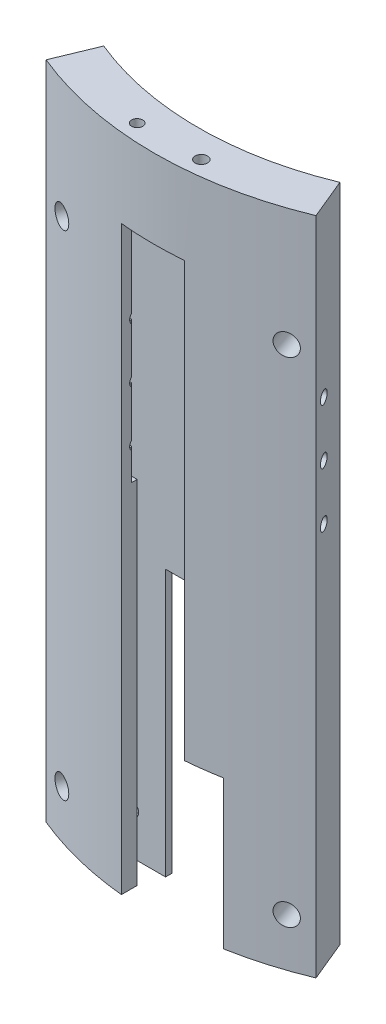
SolidWorks part; units mm, degrees
ref_plane "Front Plane" through (0, 0, 0) normal (0, 0, 1) x (1, 0, 0)
ref_plane "Top Plane" through (0, 0, 0) normal (0, 1, 0) x (1, 0, 0)
ref_plane "Right Plane" through (0, 0, 0) normal (1, 0, 0) x (0, 0, -1)
sketch "Sketch1" plane through (0, 0, 0) normal (0, 1, 0) x (1, 0, 0)
  line L1 (-23.1, -13.65) -> (23.1, -13.65)
  line L2 (-23.1, -13.65) -> (-23.1, 13.65)
  line L3 (-23.1, 13.65) -> (23.1, 13.65)
  line L4 (23.1, -13.65) -> (23.1, 13.65)
  line L5 (-23.1, -13.65) -> (23.1, 13.65) construction
  line L6 (-23.1, 13.65) -> (23.1, -13.65) construction
  point P0 (0, 0)
extrude "Boss-Extrude1" add sketch "Sketch1" along normal blind 107
sketch "Sketch2" plane through (0, 0, 0) normal (0, -1, 0) x (1, 0, 0)
  line L0 (-5.5, 3.65) -> (4.8, 3.65)
  line L5 (-13.1, 1.25) -> (-13.1, -2.25)
  line L6 (-4.4, -3.65) -> (13.1, -3.65)
  line L7 (-4.4, -3.65) -> (-4.4, -2.25)
  line L8 (-4.4, -2.25) -> (-13.1, -2.25)
  line L9 (13.1, -2.15) -> (13.1, -3.65)
  line L10 (-13.1, 1.25) -> (-5.5, 1.25)
  line L11 (-5.5, 1.25) -> (-5.5, 3.65)
  line L13 (4.8, 3.65) -> (4.8, 3.05)
  line L14 (4.8, 3.05) -> (10.4, 3.05)
  line L15 (10.4, 3.05) -> (10.4, 0.45)
  line L16 (10.4, 0.45) -> (11.7, 0.45)
  line L17 (11.7, 0.45) -> (11.7, -2.15)
  line L18 (11.7, -2.15) -> (13.1, -2.15)
  point P0 (0, 0)
extrude "Cut-Extrude1" cut sketch "Sketch2" against normal blind 24
sketch "Sketch3" plane through (0, 24, 0) normal (0, -1, 0) x (1, 0, 0)
  line L0 (-13.1, 1.25) -> (-13.1, -2.25)
  line L1 (-13.1, -2.25) -> (-4.4, -2.25)
  line L2 (-4.4, -2.25) -> (-4.4, -3.65)
  line L3 (-4.4, -3.65) -> (13.1, -3.65)
  line L4 (13.1, -3.65) -> (13.1, -2.15)
  line L5 (13.1, -2.15) -> (11.7, -2.15)
  line L6 (11.7, 0.45) -> (10.4, 0.45)
  line L7 (11.7, 0.45) -> (11.7, -2.15)
  line L8 (10.4, 0.45) -> (10.4, 2.15)
  line L10 (10.4, 0.45) -> (10.4, 3.05) construction
  line L11 (10.4, 2.15) -> (4.8, 2.15)
  line L12 (4.8, 2.15) -> (4.8, 3.65)
  line L13 (4.8, 3.65) -> (-5.5, 3.65)
  line L14 (-5.5, 3.65) -> (-5.5, 1.25)
  line L15 (-13.1, 1.25) -> (-5.5, 1.25)
extrude "Cut-Extrude2" cut sketch "Sketch3" against normal blind 19.2
sketch "Sketch4" plane through (0, 43.2, 0) normal (0, -1, 0) x (1, 0, 0)
  line L0 (-13.1, -2.25) -> (11.7, -2.25)
  line L1 (-13.1, -2.25) -> (-13.1, -0.55)
  line L2 (-13.1, 1.25) -> (-13.1, -2.25) construction
  line L3 (-13.1, -0.55) -> (-9.3, -0.55)
  line L4 (-9.3, -0.55) -> (-9.3, 1.25)
  line L5 (-9.3, 1.25) -> (-5.5, 1.25)
  line L6 (-5.5, 1.25) -> (-5.5, 3.65)
  line L7 (-5.5, 3.65) -> (4.8, 3.65)
  line L8 (4.8, 3.65) -> (4.8, 1.15)
  line L9 (4.8, 1.15) -> (8.9, 1.15)
  line L10 (8.9, 1.15) -> (8.9, -0.55)
  line L11 (8.9, -0.55) -> (11.7, -0.55)
  line L12 (11.7, -2.15) -> (11.7, 0.45) construction
  line L13 (11.7, -0.55) -> (11.7, -2.25)
extrude "Cut-Extrude3" cut sketch "Sketch4" against normal blind 50
sketch "Sketch5" plane through (0, 93.2, 0) normal (0, -1, 0) x (1, 0, 0)
  line L0 (-13.1, -2.25) -> (11.7, -2.25)
  line L1 (11.7, -2.25) -> (11.7, -0.55)
  line L2 (-5.5, 3.65) -> (4.8, 3.65)
  line L3 (4.8, 3.65) -> (4.8, -0.55)
  line L4 (4.8, -0.55) -> (11.7, -0.55)
  line L5 (-5.5, 3.65) -> (-5.5, -0.55)
  line L6 (-5.5, -0.55) -> (-13.1, -0.55)
  line L7 (-13.1, -0.55) -> (-13.1, -2.25)
extrude "Cut-Extrude4" cut sketch "Sketch5" against normal blind 1
sketch "Sketch6" plane through (0, 94.2, 0) normal (0, -1, 0) x (1, 0, 0)
  line L1 (-13.1, -0.55) -> (11.7, -0.55)
  line L2 (-13.1, -0.55) -> (-13.1, -2.25)
  line L3 (-13.1, -2.25) -> (11.7, -2.25)
  line L4 (11.7, -0.55) -> (11.7, -2.25)
extrude "Cut-Extrude5" cut sketch "Sketch6" against normal blind 5.48
fillet "Fillet1" radius 3.1 2 edges at (11.7, 99.68, -1.4) (-13.1, 99.68, -1.4)
sketch "Sketch7" plane through (-23.1, 0, 0) normal (-1, 0, 0) x (0, 0, 1)
  line L1 (13.65, 107) -> (-13.65, 107)
  line L2 (13.65, 107) -> (13.65, 0)
  line L3 (13.65, 0) -> (-13.65, 0)
  line L4 (-13.65, 107) -> (-13.65, 0)
extrude "Boss-Extrude2" add sketch "Sketch7" along normal blind 35.75
sketch "Sketch8" plane through (23.1, 0, 0) normal (1, 0, 0) x (0, 0, -1)
  line L1 (-13.65, 107) -> (13.65, 107)
  line L2 (-13.65, 107) -> (-13.65, 0)
  line L3 (-13.65, 0) -> (13.65, 0)
  line L4 (13.65, 107) -> (13.65, 0)
extrude "Boss-Extrude3" add sketch "Sketch8" along normal blind 35.75
sketch "Sketch9" plane through (0, 0, -13.65) normal (0, 0, -1) x (-1, 0, 0)
  line L1 (-58.85, 0) -> (58.85, 0)
  line L2 (-58.85, 0) -> (-58.85, 107)
  line L3 (-58.85, 107) -> (58.85, 107)
  line L4 (58.85, 0) -> (58.85, 107)
extrude "Boss-Extrude4" add sketch "Sketch9" along normal blind 39.2125
sketch "Sketch10" plane through (0, 0, 0) normal (0, -1, 0) x (1, 0, 0)
  line L2 (-19.0342, -6.8685) -> (-21.7704, -0.2628)
  line L3 (19.2342, -6.8685) -> (21.9704, -0.2628)
  arc A1 (21.9704, -0.2628) -> (-21.7704, -0.2628) centre (0.1, -53.0625) ccw
  arc A2 (19.2342, -6.8685) -> (-19.0342, -6.8685) centre (0.1, -53.0625) ccw
  dimension "D1" = 45
extrude "Cut-Extrude6" cut sketch "Sketch10" against normal up to vertex (107 mm away) flip side to cut
sketch "Sketch14" plane through (-18.6751, 0, -7.7355) normal (-0.9239, 0, -0.3827) x (-0.3827, 0, 0.9239)
  line L0 (5.7509, 80) -> (0.9384, 80)
  line L2 (-49.0616, 107) -> (-49.0616, 73.6066)
  line L3 (0.9384, 107) -> (0.9384, 0) construction
  circle A0 centre (5.7509, 80) radius 1
  circle A1 centre (5.7509, 71.1) radius 1
  circle A2 centre (5.7509, 62.2) radius 1
  dimension "D1" = 3
  dimension "D2" = 2
revolve "Cut-Revolve1" cut sketch "Sketch14" angle 360 about L2
sketch "Sketch15" plane through (0, 107, 0) normal (0, 1, 0) x (1, 0, 0)
  circle A0 centre (4.8, -1.15) radius 1
  circle A1 centre (-5.5, -1.25) radius 0.9
extrude "Cut-Extrude7" cut sketch "Sketch15" against normal blind 50
ref_plane "Plane3" through (-2.157, 0, 6.4466) normal (-0.3173, 0, 0.9483) x (0, -1, 0)
sketch "Sketch19" plane through (-18.6751, 0, -7.7355) normal (-0.9239, 0, -0.3827) x (-0.3827, 0, 0.9239)
  line L1 (-49.0616, 0) -> (-49.0616, 49.8545)
sketch "Sketch25" plane through (0, 0, -2.25) normal (0, 0, 1) x (1, 0, 0)
  circle A0 centre (-9.9075, 95.74) radius 1.15
  circle A1 centre (8.5075, 95.74) radius 1.15
  circle A2 centre (-9.9075, 6.84) radius 1.15
  dimension "D1" = 2
extrude "Cut-Extrude8" cut sketch "Sketch25" along normal blind 4.6 and the other way up to next
sketch "Sketch26" plane through (0, 0, -2.25) normal (0, 0, 1) x (1, 0, 0)
  circle A0 centre (-9.9075, 95.74) radius 1.75
  circle A1 centre (8.5075, 95.74) radius 1.75
  circle A3 centre (-9.9075, 6.84) radius 1.75
ref_plane "Plane5" through (0, 0, -3.25) normal (0, 0, 1) x (1, 0, 0)
extrude "Cut-Extrude10" cut sketch "Sketch26" against normal blind 2 from surface at -1 starting at plane "Plane5"
sketch "Sketch27" plane through (0, 43.2, 0) normal (0, -1, 0) x (1, 0, 0)
  line L0 (13.1, -3.65) -> (13.1, -2.15) construction
  line L1 (13.1, -2.6638) -> (7.3167, -2.6638)
  line L2 (13.1, -2.6638) -> (13.1, -6.4346)
  line L3 (13.1, -6.4346) -> (7.3167, -6.4346)
  line L4 (7.3167, -2.6638) -> (7.3167, -6.4346)
extrude "Cut-Extrude11" cut sketch "Sketch27" along normal blind 45
sketch "Sketch28" plane through (0, 94.2, 0) normal (0, -1, 0) x (1, 0, 0)
  line L1 (-5.5, 1.25) -> (4.8, 1.25)
  line L2 (-5.5, 1.25) -> (-5.5, 6.2461)
  line L3 (-5.5, 6.2461) -> (4.8, 6.2461)
  line L4 (4.8, 1.25) -> (4.8, 6.2461)
extrude "Cut-Extrude12" cut sketch "Sketch28" along normal blind 100
sketch "Sketch29" plane through (0, 24, 0) normal (0, -1, 0) x (1, 0, 0)
  line L1 (4.8, 2.15) -> (10.4, 2.15)
  line L2 (4.8, 2.15) -> (4.8, 6.9892)
  line L3 (4.8, 6.9892) -> (10.4, 6.9892)
  line L4 (10.4, 2.15) -> (10.4, 6.9892)
extrude "Cut-Extrude13" cut sketch "Sketch29" along normal blind 30
sketch "Sketch31" plane through (-2.157, 0, 6.4466) normal (-0.3173, 0, 0.9483) x (0, -1, 0)
  circle A0 centre (-7.8169, -16.4536) radius 1.75
extrude "Cut-Extrude14" cut sketch "Sketch31" against normal through all
pattern_circular "CirPattern1" count 2 every 37 about axis through (0.1, 0, -53.0625) along (0, 1, 0) of "Cut-Extrude14"
pattern_linear "LPattern1" count 2 spacing 80 along (0, 1, 0) of "CirPattern1", "Cut-Extrude14"
